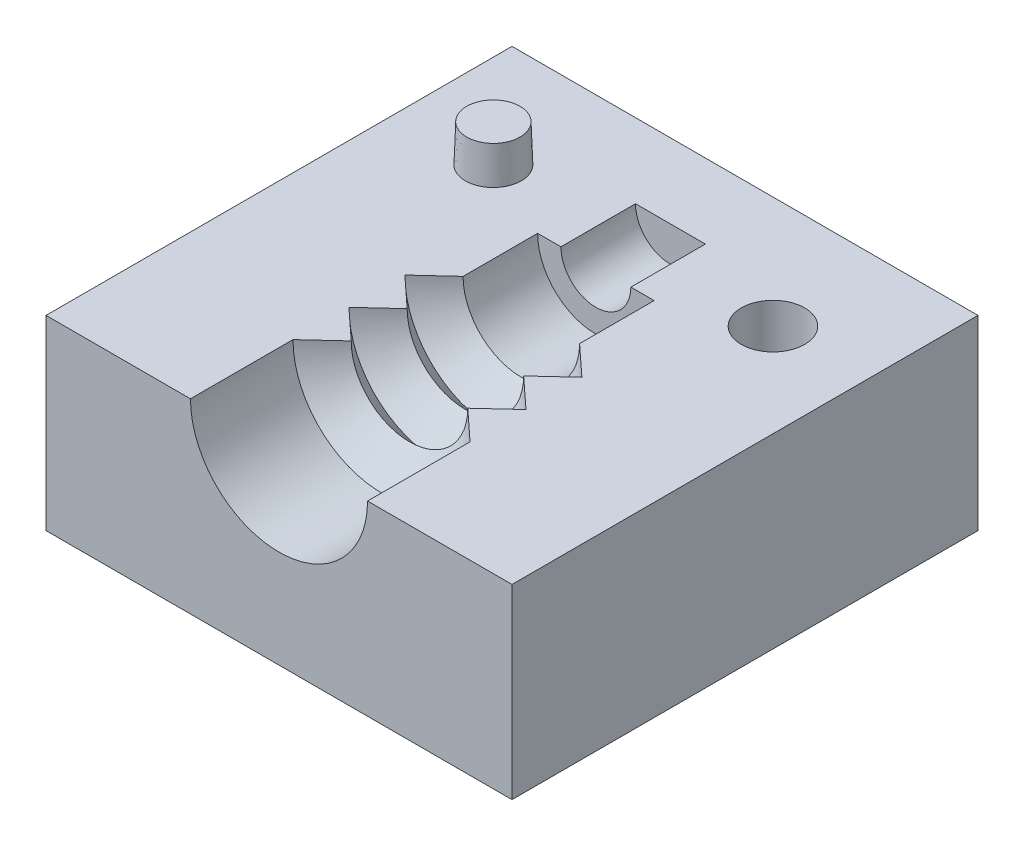
SolidWorks part; units mm, degrees
ref_plane "Front Plane" through (0, 0, 0) normal (0, 0, 1) x (1, 0, 0)
ref_plane "Top Plane" through (0, 0, 0) normal (0, 1, 0) x (1, 0, 0)
ref_plane "Right Plane" through (0, 0, 0) normal (1, 0, 0) x (0, 0, -1)
sketch "Sketch2" plane through (0, 0, 0) normal (0, 1, 0) x (1, 0, 0)
  line L0 (-12.5, 12.5) -> (12.5, -12.5) construction
  line L1 (-12.5, 12.5) -> (12.5, 12.5)
  line L2 (-12.5, 12.5) -> (-12.5, -12.5)
  line L3 (-12.5, -12.5) -> (12.5, -12.5)
  line L4 (12.5, 12.5) -> (12.5, -12.5)
  dimension "D1" = 25
  dimension "D2" = 25
extrude "Boss-Extrude1" add sketch "Sketch2" along normal blind 10
sketch "Sketch3" plane through (0, 10, 0) normal (0, 1, 0) x (1, 0, 0)
  line L0 (0, 12.5) -> (0, -12.5) construction
  line L1 (12.5, 12.5) -> (-12.5, 12.5) construction
  line L2 (-12.5, -12.5) -> (12.5, -12.5) construction
  line L3 (0, -12.5) -> (4.75, -12.5)
  line L4 (4.75, -12.5) -> (4.75, -7)
  line L5 (4.75, -7) -> (3.125, -5.5)
  line L6 (3.125, -5.5) -> (4.75, -4)
  line L7 (4.75, -4) -> (3.125, -2.5)
  line L8 (3.125, -2.5) -> (4.75, -1)
  line L9 (4.75, -1) -> (3.125, 0.5)
  line L10 (3.125, 0.5) -> (3.125, 4.5)
  line L11 (3.125, 4.5) -> (1.875, 4.5)
  line L12 (1.875, 4.5) -> (1.875, 8.5)
  line L13 (1.875, 8.5) -> (0, 8.5)
  line L14 (0, 8.5) -> (0, -12.5)
  line L15 (4.75, -7) -> (4.75, -4) construction
  line L16 (4.75, -1) -> (4.75, -4) construction
  line L17 (3.125, -2.5) -> (3.125, 0.5) construction
  line L18 (3.125, -2.5) -> (3.125, -5.5) construction
  line L19 (3.125, -5.5) -> (4.75, -5.5) construction
  line L20 (4.75, -4) -> (3.125, -4) construction
  line L21 (3.125, -2.5) -> (4.75, -2.5) construction
  line L22 (4.75, -1) -> (3.125, -1) construction
  point P6 (3.125, -7.7587)
  point P22 (0.933, 7.8359)
  dimension "D1" = 9.5
  dimension "D2" = 6.25
  dimension "D3" = 3
  dimension "D4" = 5.5
  dimension "D5" = 4
  dimension "D6" = 1.25
  dimension "D7" = 4
revolve "Cut-Revolve1" cut sketch "Sketch3" angle 360 about L0
sketch "Sketch4" plane through (0, 10, 0) normal (0, 1, 0) x (1, 0, 0)
  line L0 (-7.5, 6.5) -> (-12.5, 6.5) construction
  line L1 (-12.5, 12.5) -> (-12.5, -12.5) construction
  line L2 (12.5, 12.5) -> (-12.5, 12.5) construction
  circle A0 centre (-7.5, 6.5) radius 1.5
  dimension "D3" = 3
  dimension "D1" = 5
  dimension "D2" = 6
extrude "Boss-Extrude2" add sketch "Sketch4" along normal blind 2 draft 2
sketch "Sketch5" plane through (0, 10, 0) normal (0, 1, 0) x (1, 0, 0)
  line L0 (-7.5, 6.5) -> (7.5, 6.5) construction
  line L1 (0, 6.5) -> (0, 0) construction
  circle A0 centre (7.5, 6.5) radius 1.5 construction
  circle A1 centre (-7.5, 6.5) radius 1.5 construction
  circle A2 centre (7.5, 6.5) radius 1.7
  dimension "D1" = 0.2
extrude "Cut-Extrude1" cut sketch "Sketch5" against normal blind 2.5
